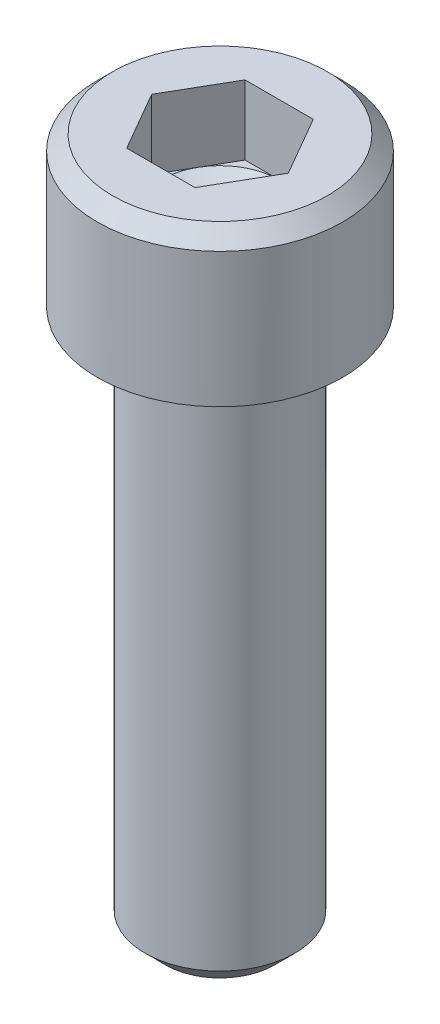
SolidWorks part; units mm, degrees
material "Alloy Steel"
ref_plane "Front Plane" through (0, 0, 0) normal (0, 0, 1) x (1, 0, 0)
ref_plane "Top Plane" through (0, 0, 0) normal (0, 1, 0) x (1, 0, 0)
ref_plane "Right Plane" through (0, 0, 0) normal (1, 0, 0) x (0, 0, -1)
sketch "Sketch1" plane through (0, 0, 0) normal (0, 0, 1) x (1, 0, 0)
  line L0 (2.8702, 3.5052) -> (0, 3.5052)
  line L1 (0, 3.5052) -> (0, 0)
  line L2 (0, 0) -> (2.8702, 0)
  line L3 (2.8702, 0) -> (2.8702, 3.5052)
  line L4 (0, 3.5052) -> (0, 0) construction
revolve "Revolve1" add sketch "Sketch1" angle 360 about L4
sketch "Sketch2" plane through (0, 0, 0) normal (0, -1, 0) x (1, 0, 0)
  circle A0 centre (0, 0) radius 1.7526
extrude "Boss-Extrude1" add sketch "Sketch2" along normal blind 12.7
sketch "Sketch3" plane through (0, 3.5052, 0) normal (0, 1, 0) x (-1, 0, 0)
  line L0 (-0.7992, 1.3843) -> (-1.5985, 0)
  line L1 (-1.5985, 0) -> (-0.7992, -1.3843)
  line L2 (-0.7992, -1.3843) -> (0.7992, -1.3843)
  line L3 (0.7992, -1.3843) -> (1.5985, 0)
  line L4 (1.5985, 0) -> (0.7992, 1.3843)
  line L5 (0.7992, 1.3843) -> (-0.7992, 1.3843)
extrude "Cut-Extrude1" cut sketch "Sketch3" against normal blind 1.6256
sketch "Sketch4" plane through (0, 0, 0) normal (0, 0, 1) x (1, 0, 0)
  line L0 (1.3843, 1.8796) -> (0, 1.8796)
  line L1 (0, 1.8796) -> (0, 1.0804)
  line L2 (0, 1.0804) -> (1.3843, 1.8796)
  line L3 (0, 1.8796) -> (0, 1.0803) construction
revolve "Cut-Revolve1" cut sketch "Sketch4" angle 360 about L3
chamfer "Chamfer1" distance 0.4724 angle 45 1 edges at (0, -12.7, -1.7526)
chamfer "Chamfer2" distance 0.3556 angle 45 1 edges at (0, 3.5052, -2.8702)
fillet "Fillet1" radius 0.254 1 edges at (0, 0, -1.7526)
